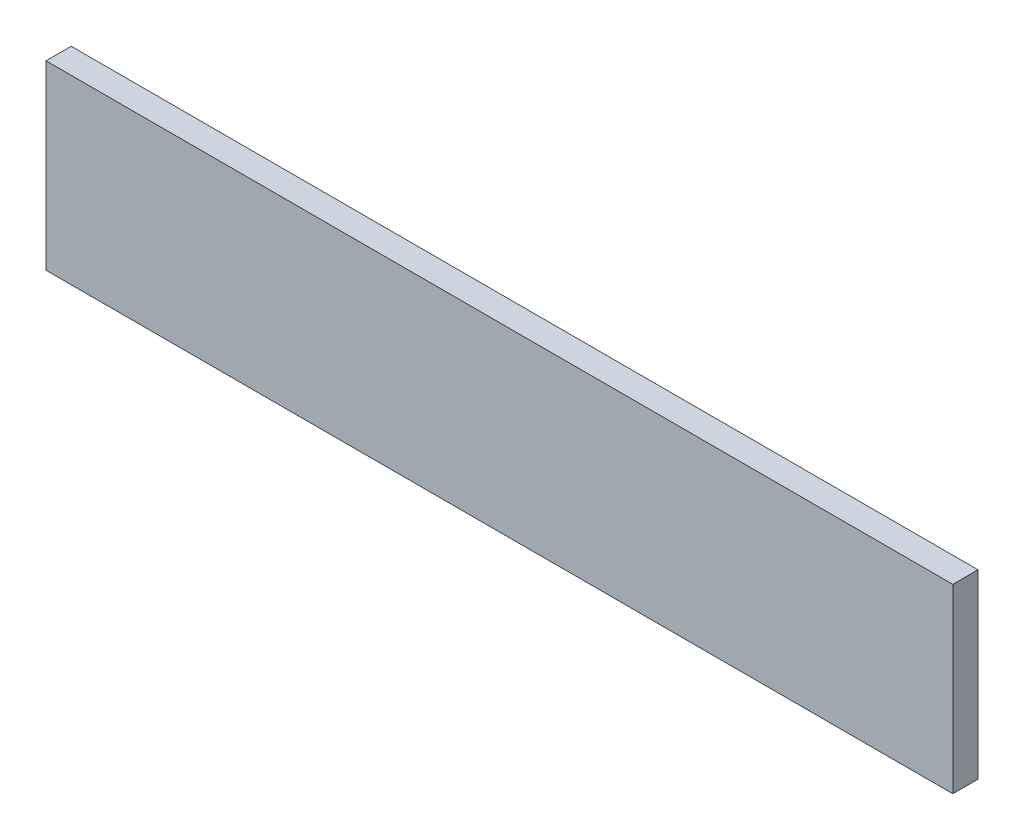
SolidWorks part; units mm, degrees
ref_plane "Front Plane" through (0, 0, 0) normal (0, 0, 1) x (1, 0, 0)
ref_plane "Top Plane" through (0, 0, 0) normal (0, 1, 0) x (1, 0, 0)
ref_plane "Right Plane" through (0, 0, 0) normal (1, 0, 0) x (0, 0, -1)
sketch "Sketch1" plane through (0, 0, 0) normal (0, 0, 1) x (1, 0, 0)
  line L1 (-57.15, -11.43) -> (57.15, -11.43)
  line L2 (-57.15, -11.43) -> (-57.15, 11.43)
  line L3 (-57.15, 11.43) -> (57.15, 11.43)
  line L4 (57.15, -11.43) -> (57.15, 11.43)
  line L5 (-57.15, -11.43) -> (57.15, 11.43) construction
  line L6 (-57.15, 11.43) -> (57.15, -11.43) construction
  point P0 (0, 0)
  dimension "D1" = 22.86
  dimension "D2" = 114.3
extrude "Boss-Extrude1" add sketch "Sketch1" along normal mid plane 3.175
